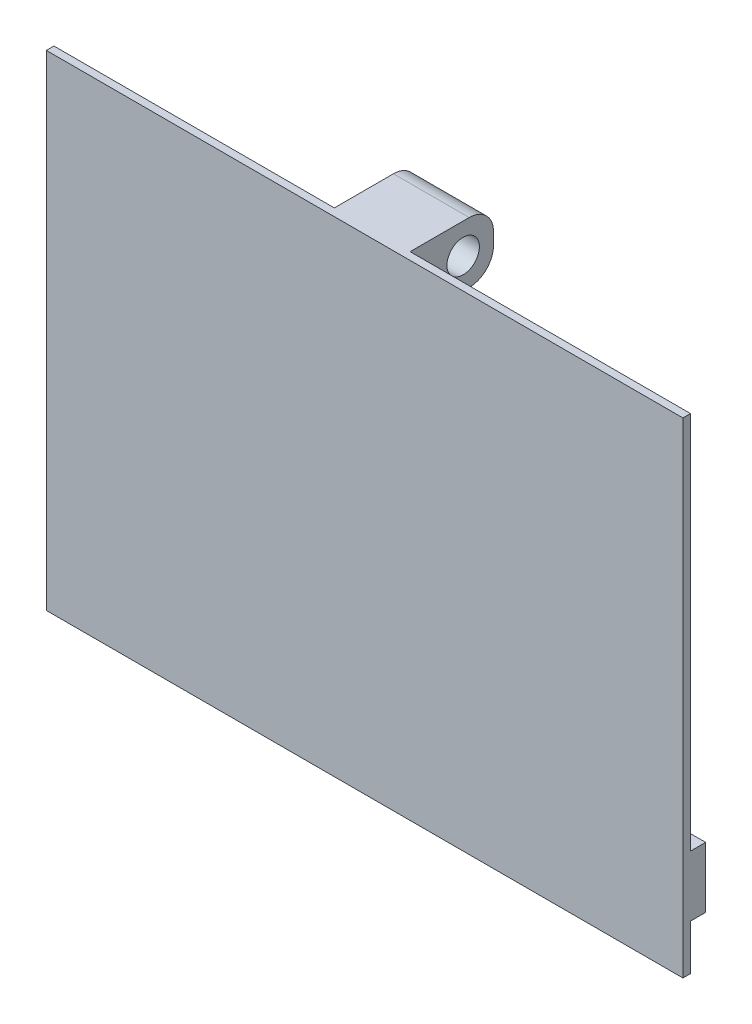
SolidWorks part; units mm, degrees
ref_plane "Front Plane" through (0, 0, 0) normal (0, 0, 1) x (1, 0, 0)
ref_plane "Top Plane" through (0, 0, 0) normal (0, 1, 0) x (1, 0, 0)
ref_plane "Right Plane" through (0, 0, 0) normal (1, 0, 0) x (0, 0, -1)
sketch "Sketch1" plane through (0, 0, 0) normal (0, 0, 1) x (1, 0, 0)
  line L1 (-33.3375, -25.4) -> (33.3375, -25.4)
  line L2 (-33.3375, -25.4) -> (-33.3375, 25.4)
  line L3 (-33.3375, 25.4) -> (33.3375, 25.4)
  line L4 (33.3375, -25.4) -> (33.3375, 25.4)
  line L5 (-33.3375, -25.4) -> (33.3375, 25.4) construction
  line L6 (-33.3375, 25.4) -> (33.3375, -25.4) construction
  point P0 (0, 0)
  dimension "D1" = 50.8
  dimension "D2" = 66.675
extrude "Boss-Extrude1" add sketch "Sketch1" along normal blind 0.7937
sketch "Sketch3" plane through (0, 0, 0) normal (1, 0, 0) x (0, 0, -1)
  line L1 (0, 25.4) -> (6.1912, 25.4)
  line L2 (0, 25.4) -> (0, 19.05)
  line L3 (0, 19.05) -> (6.1912, 19.05)
  line L4 (0, -25.4) -> (0, 25.4)
  line L5 (-0.7937, -25.4) -> (0, -25.4)
  line L6 (-0.7937, 25.4) -> (-0.7937, -25.4)
  line L7 (0, 25.4) -> (-0.7937, 25.4)
  line L8 (0, -25.4) -> (0, 25.4) construction
  line L9 (-0.7937, -25.4) -> (0, -25.4) construction
  line L10 (-0.7937, 25.4) -> (-0.7937, -25.4) construction
  line L11 (0, 25.4) -> (-0.7937, 25.4) construction
  line L12 (8.7312, 22.86) -> (8.7312, 21.59)
  arc A0 (6.1912, 19.05) -> (8.7312, 21.59) centre (6.1913, 21.59) ccw
  arc A1 (6.1912, 25.4) -> (8.7312, 22.86) centre (6.1913, 22.86) cw
  point P7 (5.5562, 22.225)
  dimension "D6" = 2.54
  dimension "D2" = 5.5562
  dimension "D3" = 3.175
  dimension "D4" = 3.175
  dimension "D5" = 3.175
  dimension "D1" = 0
extrude "Boss-Extrude2" add sketch "Sketch3" along normal mid plane 7.9375
hole_wizard "M3 Clearance Hole1" positions "Sketch6" profile "Sketch8" hole size "M3" standard "ANSI Metric"
sketch "Sketch6" plane through (0, 0, 0) normal (1, 0, 0) x (0, 0, -1)
  point P0 (5.5562, 22.225)
sketch "Sketch8" plane through (0, 22.225, -5.5562) normal (0, 1, 0) x (0, 0, -1)
  line L0 (0, 0) -> (0, 7.3715)
  line L1 (0, 7.3715) -> (1.7, 6.35)
  line L2 (1.7, 6.35) -> (1.7, 0)
  line L5 (1.7, 0) -> (0, 0)
  line L10 (0, 7.3715) -> (-1.7, 6.35) construction
  line L11 (0, -6.35) -> (0, 107.95) construction
  dimension "Hole Dia." = 3.4
  dimension "Hole Depth" = 6.35
  dimension "Drill Angle" = 118
hole_wizard "M3 Clearance Hole2" positions "Sketch9" profile "Sketch10" hole size "M3" standard "ANSI Metric"
sketch "Sketch9" plane through (0, 0, 0) normal (-1, 0, 0) x (0, 0, 1)
  point P0 (-5.5562, 22.225)
sketch "Sketch10" plane through (0, 22.225, -5.5562) normal (0, 1, 0) x (0, 0, 1)
  line L0 (0, 0) -> (0, 7.3715)
  line L1 (0, 7.3715) -> (1.7, 6.35)
  line L2 (1.7, 6.35) -> (1.7, 0)
  line L5 (1.7, 0) -> (0, 0)
  line L10 (0, 7.3715) -> (-1.7, 6.35) construction
  line L11 (0, -6.35) -> (0, 107.95) construction
  dimension "Hole Dia." = 3.4
  dimension "Hole Depth" = 6.35
  dimension "Drill Angle" = 118
sketch "Sketch11" plane through (0, 0, 0) normal (0, 0, -1) x (-1, 0, 0)
  line L0 (-33.3375, -25.4) -> (-33.3375, 25.4) construction
  line L1 (-33.3375, -14.2875) -> (33.3375, -14.2875)
  line L2 (-33.3375, -14.2875) -> (-33.3375, -20.6375)
  line L3 (-33.3375, -20.6375) -> (33.3375, -20.6375)
  line L4 (33.3375, -14.2875) -> (33.3375, -20.6375)
  line L5 (33.3375, 25.4) -> (33.3375, -25.4) construction
  line L6 (33.3375, -25.4) -> (-33.3375, -25.4) construction
  dimension "D1" = 6.35
  dimension "D2" = 4.7625
extrude "Boss-Extrude3" add sketch "Sketch11" along normal blind 1.5875
